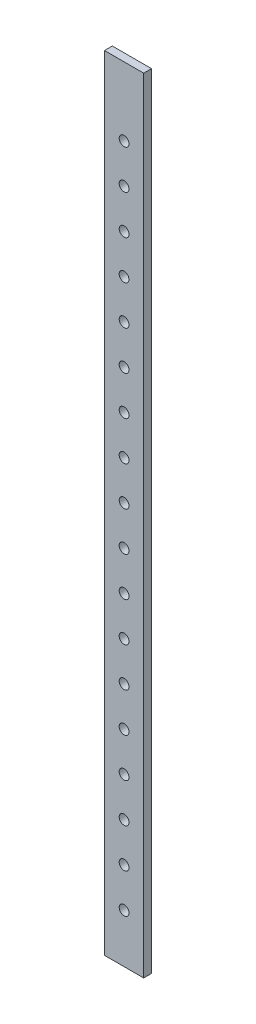
SolidWorks part; units mm, degrees
ref_plane "Спереди" through (0, 0, 0) normal (0, 0, 1) x (1, 0, 0)
ref_plane "Сверху" through (0, 0, 0) normal (0, 1, 0) x (1, 0, 0)
ref_plane "Справа" through (0, 0, 0) normal (1, 0, 0) x (0, 0, -1)
sketch "Эскиз1" plane through (0, 0, 0) normal (0, 1, 0) x (1, 0, 0)
  line L1 (-10, 2) -> (10, 2)
  line L2 (-10, 2) -> (-10, -2)
  line L3 (-10, -2) -> (10, -2)
  line L4 (10, 2) -> (10, -2)
  line L5 (-10, 2) -> (10, -2) construction
  line L6 (-10, -2) -> (10, 2) construction
  point P0 (0, 0)
extrude "Бобышка-Вытянуть1" add sketch "Эскиз1" along normal blind 400
sketch "Эскиз2" plane through (0, 0, 2) normal (0, 0, 1) x (1, 0, 0)
  circle A0 centre (0, 25) radius 2.5
  circle A1 centre (0, 45) radius 2.5
  circle A2 centre (0, 65) radius 2.5
  circle A3 centre (0, 85) radius 2.5
  circle A4 centre (0, 105) radius 2.5
  circle A5 centre (0, 125) radius 2.5
  circle A6 centre (0, 145) radius 2.5
  circle A7 centre (0, 165) radius 2.5
  circle A8 centre (0, 185) radius 2.5
  circle A9 centre (0, 205) radius 2.5
  circle A10 centre (0, 225) radius 2.5
  circle A11 centre (0, 245) radius 2.5
  circle A12 centre (0, 265) radius 2.5
  circle A13 centre (0, 285) radius 2.5
  circle A14 centre (0, 305) radius 2.5
  circle A15 centre (0, 325) radius 2.5
  circle A16 centre (0, 345) radius 2.5
  circle A17 centre (0, 365) radius 2.5
  dimension "D1" = 18
extrude "Вырез-Вытянуть1" cut sketch "Эскиз2" against normal through all
